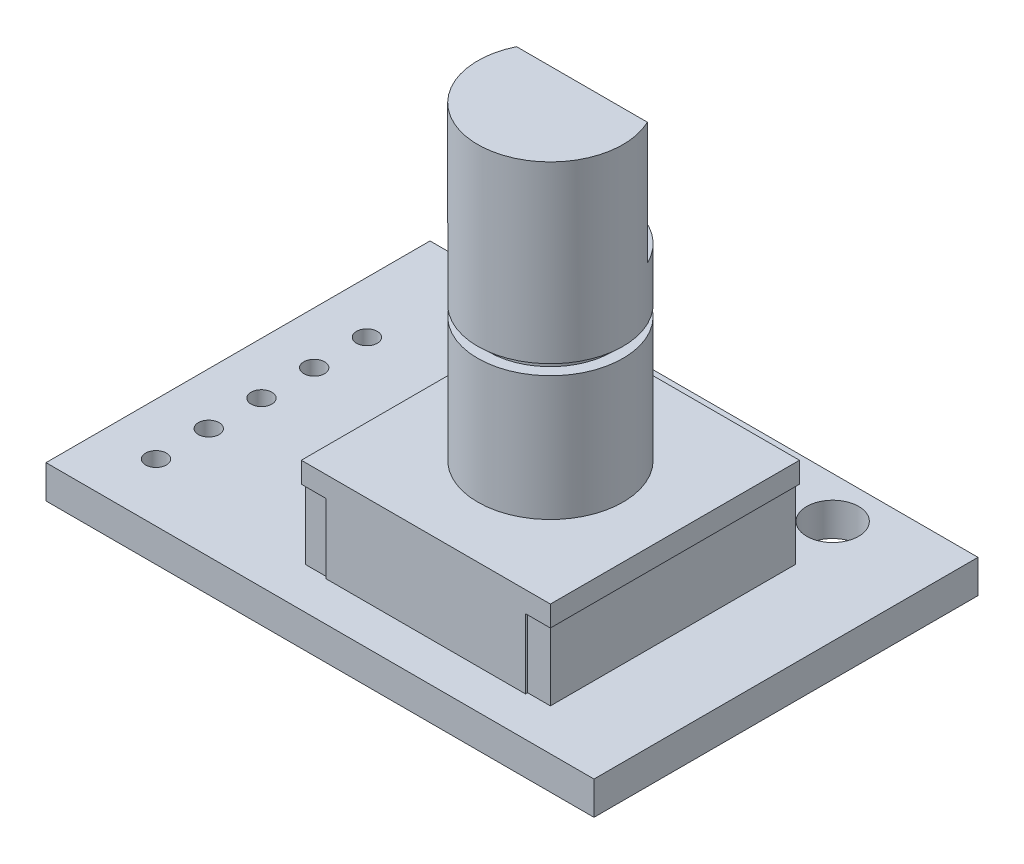
SolidWorks part; units mm, degrees
ref_plane "Front Plane" through (0, 0, 0) normal (0, 0, 1) x (1, 0, 0)
ref_plane "Top Plane" through (0, 0, 0) normal (0, 1, 0) x (1, 0, 0)
ref_plane "Right Plane" through (0, 0, 0) normal (1, 0, 0) x (0, 0, -1)
sketch "Sketch1" plane through (0, 0, 0) normal (0, 1, 0) x (1, 0, 0)
  line L1 (-13.2, -9.25) -> (13.2, -9.25)
  line L2 (-13.2, -9.25) -> (-13.2, 9.25)
  line L3 (-13.2, 9.25) -> (13.2, 9.25)
  line L4 (13.2, -9.25) -> (13.2, 9.25)
  line L5 (-13.2, -9.25) -> (13.2, 9.25) construction
  line L6 (-13.2, 9.25) -> (13.2, -9.25) construction
  circle A0 centre (-5.8, 7.25) radius 1.25
  circle A1 centre (8.2, 7.25) radius 1.25
  circle A2 centre (-10.7, -6.45) radius 0.5
  circle A3 centre (-10.7, -3.91) radius 0.5
  circle A4 centre (-10.7, -1.37) radius 0.5
  circle A5 centre (-10.7, 1.17) radius 0.5
  circle A6 centre (-10.7, 3.71) radius 0.5
  point P0 (0, 0)
  dimension "D3" = 1
  dimension "D4" = 2.8
  dimension "D5" = 2.5
  dimension "D7" = 2.5
  dimension "D8" = 2.5
  dimension "D9" = 14
  dimension "D10" = 5
  dimension "D11" = 2
  dimension "D12" = 2
  dimension "D1" = 18.5
  dimension "D2" = 26.4
  dimension "D6" = 5
extrude "Boss-Extrude1" add sketch "Sketch1" along normal blind 1.6
sketch "Sketch2" plane through (0, 1.6, 0) normal (0, 1, 0) x (1, 0, 0)
  line L0 (-13.2, -9.25) -> (13.2, -9.25) construction
  line L1 (9.2, -7.35) -> (-2.8, -7.35)
  line L2 (9.2, -7.35) -> (9.2, 4.65)
  line L3 (9.2, 4.65) -> (-2.8, 4.65)
  line L4 (-2.8, -7.35) -> (-2.8, 4.65)
  line L5 (13.2, -9.25) -> (13.2, 9.25) construction
  dimension "D1" = 12
  dimension "D2" = 12
  dimension "D3" = 1.9
  dimension "D4" = 4
extrude "Boss-Extrude2" add sketch "Sketch2" along normal blind 4.35
sketch "Sketch3" plane through (0, 1.6, 0) normal (0, 1, 0) x (1, 0, 0)
  line L0 (-1.6, 4.65) -> (-2.8, 4.65)
  line L1 (9.2, 4.65) -> (-2.8, 4.65) construction
  line L2 (-2.8, 4.65) -> (-2.8, -7.35)
  line L3 (-2.8, -7.35) -> (-1.6, -7.35)
  line L4 (-2.8, -7.35) -> (9.2, -7.35) construction
  line L5 (-1.6, -7.35) -> (-1.6, -7.25)
  line L6 (-1.6, -7.25) -> (-2.7, -7.25)
  line L7 (-2.7, -7.25) -> (-2.7, 4.55)
  line L8 (-2.7, 4.55) -> (-1.6, 4.55)
  line L9 (-1.6, 4.55) -> (-1.6, 4.65)
  line L10 (3.2, 4.65) -> (3.2, -7.35) construction
  line L11 (-2.8, -7.35) -> (9.2, -7.35) construction
  line L12 (8, -7.35) -> (8, -7.25)
  line L13 (8, -7.25) -> (9.1, -7.25)
  line L14 (9.2, -7.35) -> (8, -7.35)
  line L15 (9.1, 4.55) -> (8, 4.55)
  line L16 (8, 4.65) -> (9.2, 4.65)
  line L17 (8, 4.55) -> (8, 4.65)
  line L18 (9.2, 4.65) -> (9.2, -7.35)
  line L19 (9.1, -7.25) -> (9.1, 4.55)
  point P13 (-1.6, -7.3)
  dimension "D1" = 1.2
  dimension "D2" = 1.2
  dimension "D3" = 0.1
  dimension "D4" = 0.1
  dimension "D5" = 0.1
extrude "Cut-Extrude1" cut sketch "Sketch3" along normal blind 3.35
sketch "Sketch4" plane through (0, 5.95, 0) normal (0, 1, 0) x (1, 0, 0)
  circle A0 centre (3.2, -1.35) radius 3.5
  dimension "D1" = 7
extrude "Boss-Extrude3" add sketch "Sketch4" along normal blind 6
sketch "Sketch5" plane through (0, 11.95, 0) normal (0, 1, 0) x (1, 0, 0)
  circle A0 centre (3.2, -1.35) radius 2.9671
extrude "Boss-Extrude4" add sketch "Sketch5" along normal blind 0.5
sketch "Sketch6" plane through (0, 12.45, 0) normal (0, 1, 0) x (1, 0, 0)
  circle A0 centre (3.2, -1.35) radius 3.5
extrude "Boss-Extrude5" add sketch "Sketch6" along normal blind 2.54
sketch "Sketch7" plane through (0, 14.99, 0) normal (0, 1, 0) x (1, 0, 0)
  line L0 (0.0473, 0.17) -> (6.3527, 0.17)
  arc A0 (0.0473, 0.17) -> (6.3527, 0.17) centre (3.2, -1.35) ccw
  dimension "D1" = 1.52
extrude "Boss-Extrude6" add sketch "Sketch7" along normal blind 5.88
